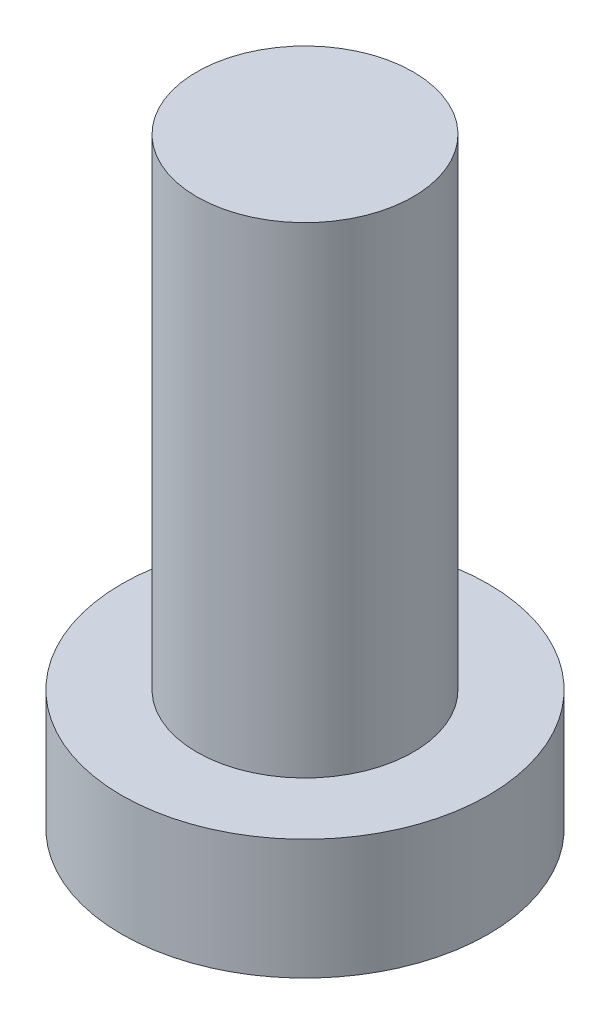
SolidWorks part; units mm, degrees
ref_plane "Front Plane" through (0, 0, 0) normal (0, 0, 1) x (1, 0, 0)
ref_plane "Top Plane" through (0, 0, 0) normal (0, 1, 0) x (1, 0, 0)
ref_plane "Right Plane" through (0, 0, 0) normal (1, 0, 0) x (0, 0, -1)
sketch "Sketch1" plane through (0, 0, 0) normal (0, 1, 0) x (1, 0, 0)
  circle A0 centre (0, 0) radius 3.81
  dimension "D1" = 7.62
extrude "Boss-Extrude1" add sketch "Sketch1" along normal blind 2.5
sketch "Sketch2" plane through (0, 2.5, 0) normal (0, 1, 0) x (1, 0, 0)
  circle A0 centre (0, 0) radius 2.25
  dimension "D1" = 4.5
extrude "Boss-Extrude2" add sketch "Sketch2" along normal blind 10
